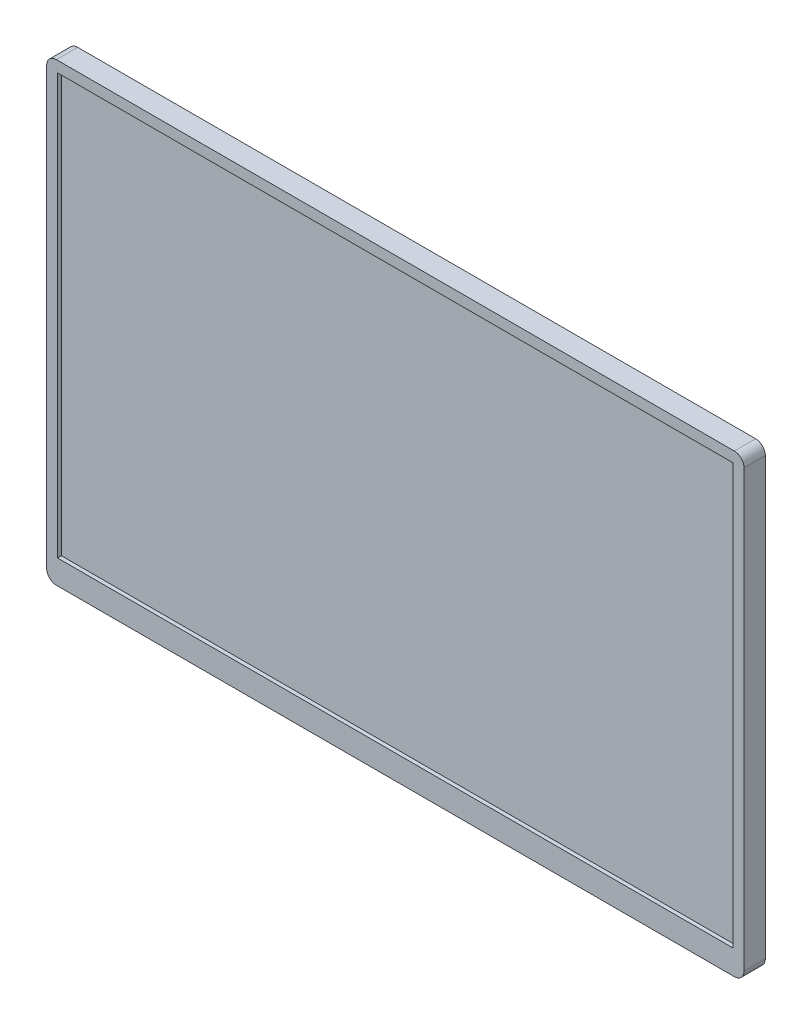
SolidWorks part; units mm, degrees
ref_plane "Front Plane" through (0, 0, 0) normal (0, 0, 1) x (1, 0, 0)
ref_plane "Top Plane" through (0, 0, 0) normal (0, 1, 0) x (1, 0, 0)
ref_plane "Right Plane" through (0, 0, 0) normal (1, 0, 0) x (0, 0, -1)
sketch "Sketch1" plane through (0, 0, 0) normal (0, 0, 1) x (1, 0, 0)
  line L1 (-180, 117.5) -> (180, 117.5)
  line L2 (-180, 117.5) -> (-180, -117.5)
  line L3 (-180, -117.5) -> (180, -117.5)
  line L4 (180, 117.5) -> (180, -117.5)
  line L5 (-180, 117.5) -> (180, -117.5) construction
  line L6 (-180, -117.5) -> (180, 117.5) construction
  point P0 (0, 0)
  dimension "D1" = 360
  dimension "D2" = 235
extrude "Boss-Extrude1" add sketch "Sketch1" along normal blind 11
fillet "Fillet1" radius 5 4 edges at (-180, 117.5, 5.5) (-180, -117.5, 5.5) (180, -117.5, 5.5) (180, 117.5, 5.5)
sketch "Sketch2" plane through (0, 0, 11) normal (0, 0, 1) x (1, 0, 0)
  line L0 (175, 117.5) -> (-175, 117.5) construction
  line L1 (-174.4, 111.9) -> (174.4, 111.9)
  line L2 (-174.4, 111.9) -> (-174.4, -105)
  line L3 (-174.4, -105) -> (174.4, -105)
  line L4 (174.4, 111.9) -> (174.4, -105)
  line L5 (180, -112.5) -> (180, 112.5) construction
  line L6 (-180, 112.5) -> (-180, -112.5) construction
  line L7 (-175, -117.5) -> (175, -117.5) construction
  dimension "D1" = 5.6
  dimension "D2" = 5.6
  dimension "D3" = 5.6
  dimension "D4" = 12.5
extrude "Cut-Extrude1" cut sketch "Sketch2" against normal blind 2
sketch "Sketch3" plane through (0, 0, 9) normal (0, 0, 1) x (1, 0, 0)
  line L0 (37.9736, 253.9818) -> (891.3069, 253.9818) construction
